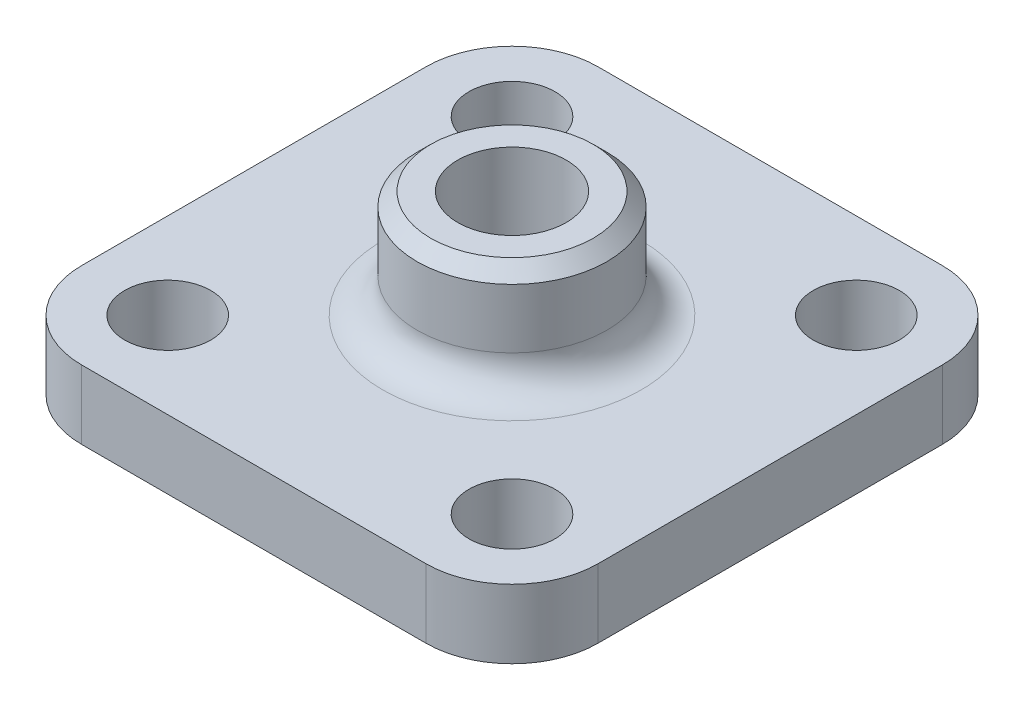
SolidWorks part; units mm, degrees
material "ABS"
ref_plane "Front Plane" through (0, 0, 0) normal (0, 0, 1) x (1, 0, 0)
ref_plane "Top Plane" through (0, 0, 0) normal (0, 1, 0) x (1, 0, 0)
ref_plane "Right Plane" through (0, 0, 0) normal (1, 0, 0) x (0, 0, -1)
sketch "Sketch1" plane through (0, 0, 0) normal (0, 1, 0) x (1, 0, 0)
  line L1 (-19.05, -19.05) -> (19.05, -19.05)
  line L2 (-19.05, -19.05) -> (-19.05, 19.05)
  line L3 (-19.05, 19.05) -> (19.05, 19.05)
  line L4 (19.05, -19.05) -> (19.05, 19.05)
  line L5 (-19.05, -19.05) -> (19.05, 19.05) construction
  line L6 (-19.05, 19.05) -> (19.05, -19.05) construction
  circle A0 centre (0, 0) radius 4
  point P0 (0, 0)
  dimension "D3" = 8
  dimension "D1" = 38.1
  dimension "D2" = 38.1
extrude "Boss-Extrude1" add sketch "Sketch1" along normal blind 5.08
sketch "Sketch2" plane through (0, 5.08, 0) normal (0, 1, 0) x (1, 0, 0)
  line L0 (19.05, -19.05) -> (19.05, 19.05) construction
  line L1 (19.05, 19.05) -> (-19.05, 19.05) construction
  point P0 (12.7, 12.7)
  point P1 (12.7, -12.7)
  point P2 (-12.7, -12.7)
  point P3 (-12.7, 12.7)
  dimension "D1" = 25.4
  dimension "D2" = 25.4
  dimension "D3" = 6.35
  dimension "D4" = 6.35
hole_wizard "1/4 (0.25) Diameter Hole1" positions "Sketch3" profile "Sketch4" hole size "1/4" standard "ANSI Inch" end condition through all
sketch "Sketch3" plane through (0, 5.08, 0) normal (0, 1, 0) x (1, 0, 0)
  point P0 (-12.7, 12.7)
  point P3 (12.7, 12.7)
  point P6 (12.7, -12.7)
  point P9 (-12.7, -12.7)
sketch "Sketch4" plane through (-12.7, 5.08, -12.7) normal (1, 0, 0) x (0, 0, 1)
  line L0 (0, 0) -> (0, 5.08)
  line L1 (0, 5.08) -> (3.175, 5.08)
  line L2 (3.175, 5.08) -> (3.175, 0)
  line L5 (3.175, 0) -> (0, 0)
  line L11 (0, -6.35) -> (0, 107.95) construction
  dimension "Thru Hole Dia." = 6.35
  dimension "Thru Hole Depth" = 5.08
sketch "Sketch5" plane through (0, 5.08, 0) normal (0, 1, 0) x (1, 0, 0)
  circle A0 centre (0, 0) radius 7
  circle A1 centre (0, 0) radius 4 construction
  circle A2 centre (0, 0) radius 4
  dimension "D1" = 14
extrude "Boss-Extrude2" add sketch "Sketch5" along normal blind 7.92
fillet "Fillet1" radius 2.54 1 edges at (0, 5.08, -7)
chamfer "Chamfer1" distance 1 angle 45 1 edges at (0, 13, 7)
fillet "Fillet2" radius 6.35 4 edges at (-19.05, 2.54, 19.05) (19.05, 2.54, 19.05) (19.05, 2.54, -19.05) (-19.05, 2.54, -19.05)
